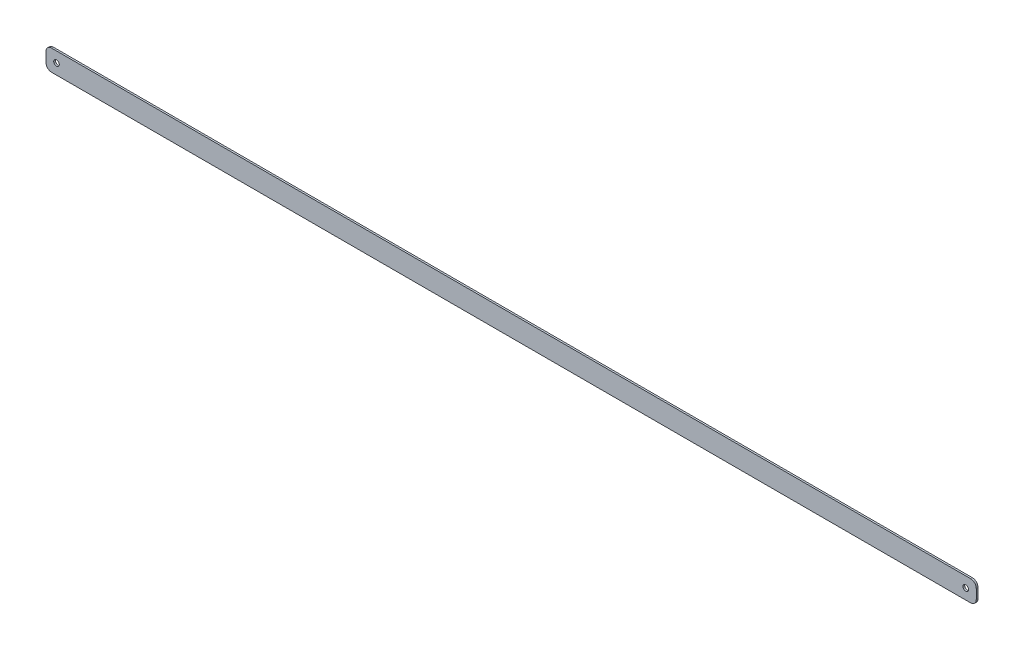
SolidWorks part; units mm, degrees
ref_plane "Front" through (0, 0, 0) normal (0, 0, 1) x (1, 0, 0)
ref_plane "Top" through (0, 0, 0) normal (0, 1, 0) x (1, 0, 0)
ref_plane "Right" through (0, 0, 0) normal (1, 0, 0) x (0, 0, -1)
sketch "Sketch1" plane through (0, 0, 0) normal (0, 0, 1) x (1, 0, 0)
  line L0 (0, 0) -> (826.1923, 0) construction
  line L1 (0, 0) -> (-9.525, 0) construction
  line L2 (-4.445, 9.525) -> (830.6373, 9.525)
  line L3 (-9.525, 4.445) -> (-9.525, -4.445)
  line L4 (-4.445, -9.525) -> (830.6373, -9.525)
  line L5 (835.7173, 4.445) -> (835.7173, -4.445)
  line L6 (-9.525, 9.525) -> (835.7173, -9.525) construction
  line L7 (-9.525, -9.525) -> (835.7173, 9.525) construction
  line L8 (826.1923, 0) -> (835.7173, 0) construction
  circle A0 centre (0, 0) radius 2.54
  circle A1 centre (826.1923, 0) radius 2.54
  arc A2 (-9.525, -4.445) -> (-4.445, -9.525) centre (-4.445, -4.445) ccw
  arc A3 (-4.445, 9.525) -> (-9.525, 4.445) centre (-4.445, 4.445) ccw
  arc A4 (830.6373, -9.525) -> (835.7173, -4.445) centre (830.6373, -4.445) ccw
  arc A5 (830.6373, 9.525) -> (835.7173, 4.445) centre (830.6373, 4.445) cw
  point P9 (413.0962, 0)
  dimension "D1" = 5.08
  dimension "D2" = 5.08
  dimension "D7" = 5.08
  dimension "D8" = 5.08
  dimension "D3" = 826.1923
  dimension "D4" = 19.05
  dimension "D5" = 9.525
  dimension "D6" = 9.525
extrude "Boss-Extrude1" add sketch "Sketch1" along normal blind 1.5875
